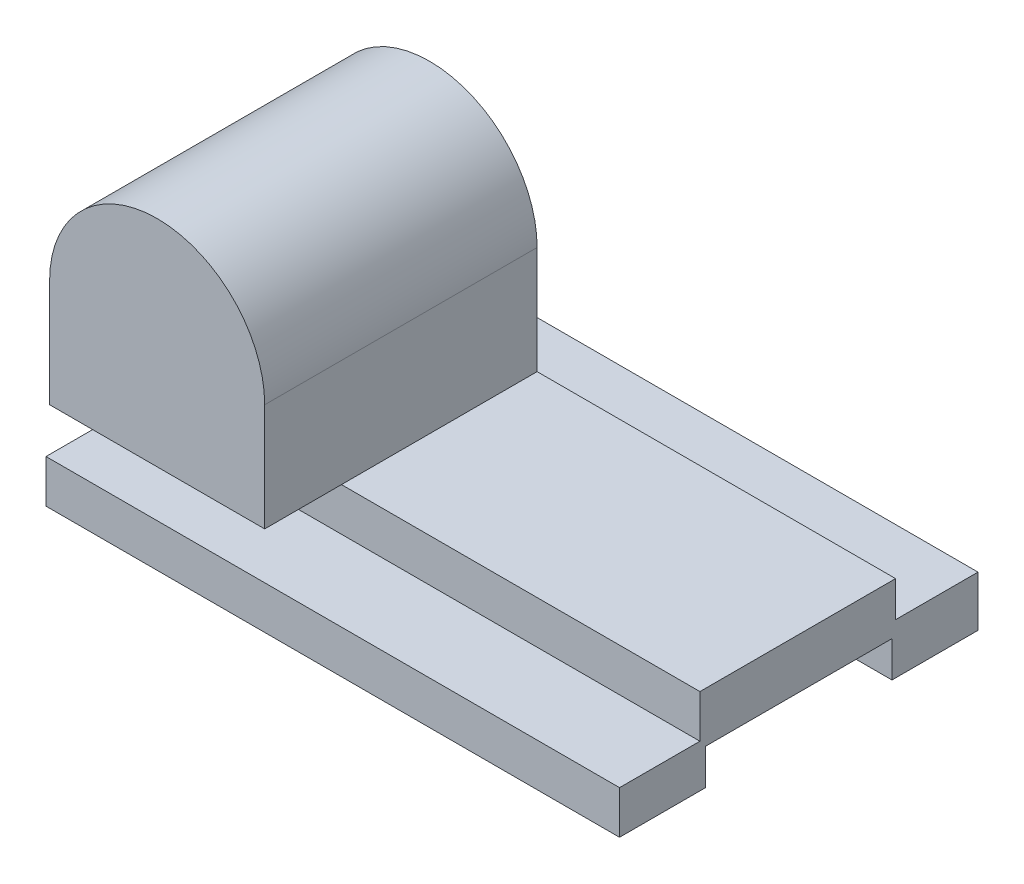
SolidWorks part; units mm, degrees
ref_plane "Front Plane" through (0, 0, 0) normal (0, 0, 1) x (1, 0, 0)
ref_plane "Top Plane" through (0, 0, 0) normal (0, 1, 0) x (1, 0, 0)
ref_plane "Right Plane" through (0, 0, 0) normal (1, 0, 0) x (0, 0, -1)
sketch "Sketch1" plane through (0, 0, 0) normal (1, 0, 0) x (0, 0, -1)
  line L0 (-26, -5) -> (-50, -5)
  line L1 (-26, 5) -> (26, 5)
  line L2 (-26, 5) -> (-26, -5)
  line L4 (26, 5) -> (26, -5)
  line L5 (-26, 5) -> (26, -5) construction
  line L6 (-26, -5) -> (26, 5) construction
  line L7 (-50, -5) -> (-50, 7)
  line L8 (-50, 7) -> (-27.5725, 7)
  line L9 (-27.5725, 7) -> (-27.5725, 19)
  line L10 (-27.5725, 19) -> (27.0076, 19)
  line L11 (27.0076, 19) -> (27.0076, 9.0763)
  line L12 (27.0076, 9.0763) -> (50, 9.0763)
  line L13 (50, 9.0763) -> (50, -5)
  line L14 (50, -5) -> (26, -5)
  point P0 (0, 0)
  dimension "D1" = 52
  dimension "D2" = 10
  dimension "D3" = 100
  dimension "D4" = 24
  dimension "D5" = 12
  dimension "D6" = 12
extrude "Boss-Extrude1" add sketch "Sketch1" against normal blind 160
sketch "Sketch2" plane through (0, 0, -27.0076) normal (0, 0, -1) x (-1, 0, 0)
  line L0 (160, 19) -> (160, 49)
  line L2 (100, 49) -> (100, 19)
  line L3 (160, 19) -> (0, 19) construction
  arc A0 (160, 49) -> (100, 49) centre (130, 49) ccw
  circle A1 centre (130, 49) radius 15
  line M8 (160, 19) -> (0, 19)
  dimension "D2" = 30
extrude "Boss-Extrude2" add sketch "Sketch2" against normal blind 76 contours L0 A0 L2 A1 M8 | A1
